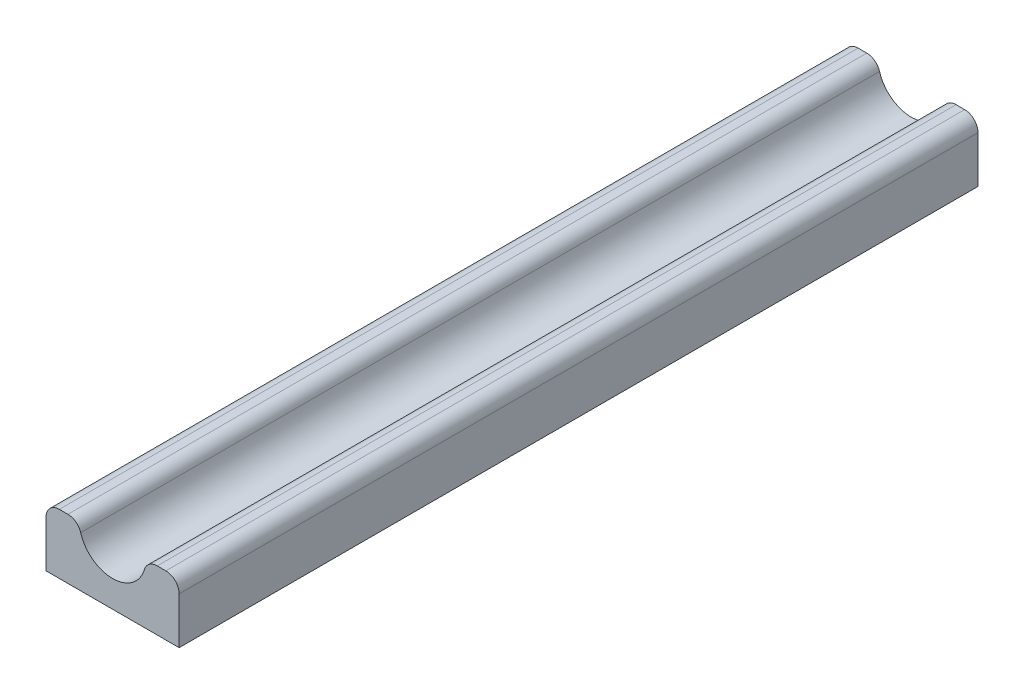
SolidWorks part; units mm, degrees
material "VITON"
ref_plane "Front" through (0, 0, 0) normal (0, 0, 1) x (1, 0, 0)
ref_plane "Top" through (0, 0, 0) normal (0, 1, 0) x (1, 0, 0)
ref_plane "Right" through (0, 0, 0) normal (1, 0, 0) x (0, 0, -1)
sketch "Sketch3" plane through (0, 0, 0) normal (0, 0, 1) x (1, 0, 0)
  line L0 (-25, 0) -> (25, 0)
  line L1 (25, 0) -> (25, 17.5)
  line L2 (20, 22.5) -> (16.7705, 22.5)
  line L3 (0, 10) -> (0, 0) construction
  line L4 (-20, 22.5) -> (-16.7705, 22.5)
  line L5 (-25, 0) -> (-25, 17.5)
  arc A0 (-11.9789, 18.9286) -> (11.9789, 18.9286) centre (0, 22.5) ccw
  arc A1 (25, 17.5) -> (20, 22.5) centre (20, 17.5) ccw
  arc A2 (16.7705, 22.5) -> (11.9789, 18.9286) centre (16.7705, 17.5) ccw
  arc A3 (-16.7705, 22.5) -> (-11.9789, 18.9286) centre (-16.7705, 17.5) cw
  arc A4 (-25, 17.5) -> (-20, 22.5) centre (-20, 17.5) cw
  point P12 (25, 22.5)
  point P15 (12.5, 22.5)
  point P20 (-12.5, 22.5)
  point P21 (-25, 22.5)
  dimension "D2" = 12.5
  dimension "D3" = 5
  dimension "D1" = 25
  dimension "D4" = 22.5
extrude "Boss-Extrude1" add sketch "Sketch3" along normal blind 300
